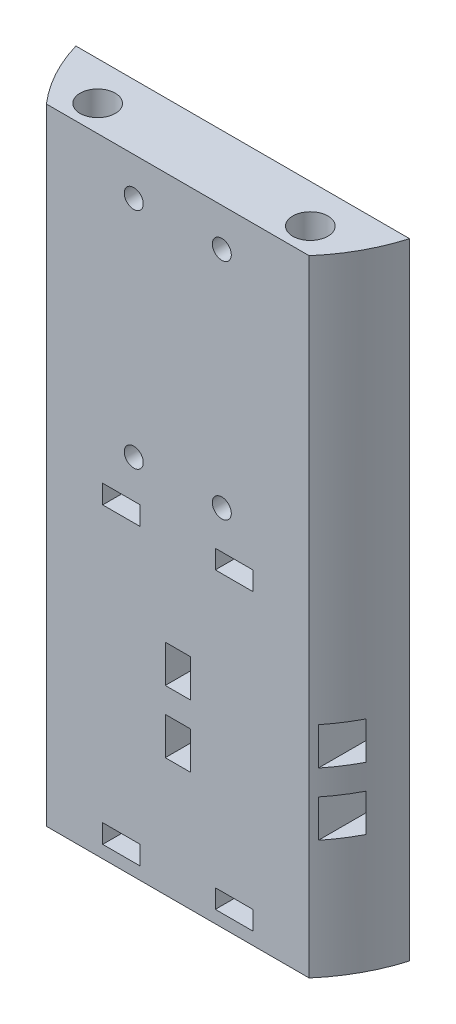
SolidWorks part; units mm, degrees
ref_plane "Front Plane" through (0, 0, 0) normal (0, 0, 1) x (1, 0, 0)
ref_plane "Top Plane" through (0, 0, 0) normal (0, 1, 0) x (1, 0, 0)
ref_plane "Right Plane" through (0, 0, 0) normal (1, 0, 0) x (0, 0, -1)
sketch "Sketch1" plane through (0, 0, 0) normal (0, 1, 0) x (1, 0, 0)
  line L0 (-33.876, -9.9465) -> (33.876, -9.9465)
  line L1 (-26.67, -23.1349) -> (26.67, -23.1349)
  arc A0 (26.67, -23.1349) -> (33.876, -9.9465) centre (0, 0) ccw
  arc A1 (-33.876, -9.9465) -> (-26.67, -23.1349) centre (0, 0) ccw
  point P1 (0, -9.9465)
  dimension "D1" = 70.612
  dimension "D4" = 35.306
  dimension "D2" = 53.34
  dimension "D3" = 67.7519
  dimension "D5" = 9.9465
extrude "Boss-Extrude1" add sketch "Sketch1" along normal blind 127
sketch "Sketch2" plane through (0, 0, 0) normal (0, 1, 0) x (1, 0, 0)
  circle A0 centre (0, 0) radius 35.306
  dimension "D1" = 70.612
sketch "Sketch3" plane through (0, 0, 0) normal (0, 1, 0) x (1, 0, 0)
  circle A0 centre (0, 0) radius 36.576
  dimension "D1" = 73.152
ref_plane "Raft Top" through (0, 0, 9.9465) normal (0, 0, -1) x (-1, 0, 0)
sketch "Sketch10" plane through (0, 0, 9.9465) normal (0, 0, -1) x (-1, 0, 0)
  line L0 (-31.336, 2.54) -> (-31.336, 66.04)
  line L5 (-31.336, 66.04) -> (31.336, 66.04)
  line L10 (31.336, 66.04) -> (31.336, 2.54)
  line L11 (31.336, 2.54) -> (-31.336, 2.54)
  line L16 (33.876, 127) -> (33.876, 0) construction
  line L17 (35.306, 0) -> (-35.306, 0) construction
  line L18 (-33.876, 127) -> (-33.876, 0) construction
  dimension "D1" = 2.54
  dimension "D2" = 2.54
  dimension "D3" = 2.54
  dimension "D4" = 63.5
  dimension "D5" = 62.6719
extrude "Cut-Extrude1" cut sketch "Sketch10" against normal blind 2.54
sketch "Sketch13" plane through (0, 127, 0) normal (0, 1, 0) x (1, 0, 0)
  line L0 (31.336, -12.4865) -> (-31.336, -12.4865) construction
  line L1 (31.336, -12.4865) -> (-31.336, -12.4865)
  line L2 (33.876, -9.9465) -> (-33.876, -9.9465)
  line L3 (-26.67, -23.1349) -> (26.67, -23.1349)
  line L4 (33.876, -9.9465) -> (-33.876, -9.9465)
  line L5 (-26.67, -23.1349) -> (26.67, -23.1349)
  line L6 (-21.59, -12.4865) -> (-21.59, -23.1349) construction
  line L7 (0, -55) -> (0, 55) construction
  arc A2 (-33.876, -9.9465) -> (-26.67, -23.1349) centre (0, 0) ccw
  arc A3 (26.67, -23.1349) -> (33.876, -9.9465) centre (0, 0) ccw
  arc A4 (-33.876, -9.9465) -> (-26.67, -23.1349) centre (0, 0) ccw
  arc A5 (26.67, -23.1349) -> (33.876, -9.9465) centre (0, 0) ccw
  point P10 (-21.59, -17.8107)
  point P13 (21.59, -17.8107)
  dimension "D2" = 21.59
  dimension "D1" = 0
hole_wizard "1/4 Clearance Hole1" positions "Sketch14" profile "Sketch15" hole size "1/4" standard "ANSI Inch" end condition through all
sketch "Sketch14" plane through (0, 127, 0) normal (0, 1, 0) x (1, 0, 0)
  point P0 (-21.59, -17.8107)
  point P3 (21.59, -17.8107)
sketch "Sketch15" plane through (-21.59, 127, 17.8107) normal (1, 0, 0) x (0, 0, 1)
  line L0 (0, 0) -> (0, 127)
  line L1 (0, 127) -> (3.5712, 127)
  line L2 (3.5712, 127) -> (3.5712, 0)
  line L5 (3.5712, 0) -> (0, 0)
  line L11 (0, -6.35) -> (0, 107.95) construction
  dimension "Thru Hole Dia." = 7.1425
  dimension "Thru Hole Depth" = 127
sketch "Sketch16" plane through (0, 0, 9.9465) normal (0, 0, -1) x (-1, 0, 0)
  line L0 (-24.939, 119.253) -> (-8.937, 73.787) construction
  line L1 (-33.876, 96.52) -> (0, 96.52) construction
  line L2 (-33.876, 127) -> (-33.876, 0) construction
  line L3 (0, 40.2336) -> (0, -40.2336) construction
  line L4 (-18.0188, 127) -> (-18.0188, 66.04) construction
  line L5 (31.336, 66.04) -> (-31.336, 66.04) construction
  point P0 (-24.939, 119.253)
  point P1 (-8.937, 119.253)
  point P2 (-8.937, 73.787)
  point P3 (-24.939, 73.787)
  point P4 (-16.938, 96.52)
  point P11 (-16.938, 96.52)
  point P26 (-18.0188, 96.52)
  point P28 (8.937, 73.787)
  point P29 (24.939, 73.787)
  point P30 (8.937, 119.253)
  point P31 (24.939, 119.253)
  dimension "D1" = 16.002
  dimension "D2" = 45.466
sketch "Sketch19" plane through (0, 0, 9.9465) normal (0, 0, -1) x (-1, 0, 0)
  line L0 (0, 66.04) -> (0, 2.54) construction
  line L1 (31.336, 66.04) -> (-31.336, 66.04) construction
  line L2 (-31.336, 2.54) -> (31.336, 2.54) construction
  line L3 (-31.336, 34.29) -> (31.336, 34.29) construction
  line L8 (-2.54, 44.45) -> (2.54, 44.45)
  line L9 (-2.54, 44.45) -> (-2.54, 36.83)
  line L10 (-2.54, 36.83) -> (2.54, 36.83)
  line L11 (2.54, 44.45) -> (2.54, 36.83)
  line L12 (-31.336, 66.04) -> (-31.336, 2.54) construction
  line L13 (31.336, 2.54) -> (31.336, 66.04) construction
  line L14 (-2.54, 31.75) -> (2.54, 31.75)
  line L15 (2.54, 24.13) -> (2.54, 31.75)
  line L16 (-2.54, 24.13) -> (2.54, 24.13)
  line L17 (-2.54, 24.13) -> (-2.54, 31.75)
  line L18 (31.336, 66.04) -> (-31.336, 66.04) construction
  line L19 (31.336, 36.83) -> (27.526, 36.83)
  line L20 (-15.24, 66.04) -> (-7.62, 66.04)
  line L21 (-15.24, 66.04) -> (-15.24, 62.23)
  line L22 (-15.24, 62.23) -> (-7.62, 62.23)
  line L23 (-7.62, 66.04) -> (-7.62, 62.23)
  line L36 (15.24, 62.23) -> (7.62, 62.23)
  line L37 (7.62, 66.04) -> (7.62, 62.23)
  line L38 (15.24, 66.04) -> (7.62, 66.04)
  line L39 (15.24, 66.04) -> (15.24, 62.23)
  line L40 (-15.24, 6.35) -> (-7.62, 6.35)
  line L41 (-7.62, 2.54) -> (-7.62, 6.35)
  line L42 (-15.24, 2.54) -> (-7.62, 2.54)
  line L43 (-15.24, 2.54) -> (-15.24, 6.35)
  line L44 (15.24, 2.54) -> (15.24, 6.35)
  line L45 (15.24, 2.54) -> (7.62, 2.54)
  line L46 (7.62, 2.54) -> (7.62, 6.35)
  line L47 (15.24, 6.35) -> (7.62, 6.35)
  line L48 (-31.336, 44.45) -> (-27.526, 44.45)
  line L49 (-31.336, 44.45) -> (-31.336, 36.83)
  line L50 (-31.336, 36.83) -> (-27.526, 36.83)
  line L51 (-27.526, 44.45) -> (-27.526, 36.83)
  line L52 (27.526, 44.45) -> (27.526, 36.83)
  line L53 (31.336, 44.45) -> (27.526, 44.45)
  line L54 (31.336, 44.45) -> (31.336, 36.83)
  line L55 (31.336, 24.13) -> (31.336, 31.75)
  line L56 (31.336, 24.13) -> (27.526, 24.13)
  line L57 (27.526, 24.13) -> (27.526, 31.75)
  line L58 (31.336, 31.75) -> (27.526, 31.75)
  line L59 (-31.336, 31.75) -> (-27.526, 31.75)
  line L60 (-27.526, 24.13) -> (-27.526, 31.75)
  line L61 (-31.336, 24.13) -> (-27.526, 24.13)
  line L62 (-31.336, 24.13) -> (-31.336, 31.75)
  point P10 (0, 34.29)
  point P12 (-2.54, 44.45)
  point P22 (-15.24, 66.04)
  point P41 (-31.336, 44.45)
  dimension "D1" = 5.08
  dimension "D2" = 7.62
  dimension "D3" = 2.54
  dimension "D4" = 10.16
  dimension "D5" = 15.24
  dimension "D6" = 7.62
  dimension "D7" = 3.81
  dimension "D8" = 10.16
  dimension "D9" = 3.81
  dimension "D10" = 7.62
hole_wizard "#8 Clearance Hole1" positions "Sketch20" profile "Sketch21" hole size "#8" standard "ANSI Inch" end condition through all
sketch "Sketch20" plane through (0, 0, 9.9465) normal (0, 0, -1) x (-1, 0, 0)
  point P3 (-8.937, 119.253)
  point P9 (-8.937, 73.787)
  point P12 (8.937, 73.787)
  point P21 (8.937, 119.253)
  point P30 (0, 0)
  point P31 (0, 0)
sketch "Sketch21" plane through (8.937, 119.253, 9.9465) normal (1, 0, 0) x (0, 1, 0)
  line L0 (0, 0) -> (0, 13.1884)
  line L1 (0, 13.1884) -> (1.9304, 13.1884)
  line L2 (1.9304, 13.1884) -> (1.9304, 0)
  line L5 (1.9304, 0) -> (0, 0)
  line L11 (0, -6.35) -> (0, 107.95) construction
  dimension "Thru Hole Dia." = 3.8608
  dimension "Thru Hole Depth" = 13.1884
extrude "Cut-Extrude3" cut sketch "Sketch19" against normal through all
hole_wizard "#8 Clearance Hole2" positions "Sketch22" profile "Sketch24" hole size "#8" standard "ANSI Inch"
sketch "Sketch22" plane through (0, 0, 9.9465) normal (0, 0, -1) x (-1, 0, 0)
  point P0 (-24.939, 119.253)
  point P3 (-24.939, 73.787)
  point P6 (24.939, 73.787)
  point P9 (24.939, 119.253)
sketch "Sketch24" plane through (24.939, 119.253, 9.9465) normal (1, 0, 0) x (0, 1, 0)
  line L0 (0, 0) -> (0, 3.81)
  line L1 (0, 3.81) -> (1.9304, 3.81)
  line L2 (1.9304, 3.81) -> (1.9304, 0)
  line L5 (1.9304, 0) -> (0, 0)
  line L10 (0, 3.81) -> (-1.9304, 3.81) construction
  line L11 (0, -6.35) -> (0, 107.95) construction
  dimension "Hole Dia." = 3.8608
  dimension "Hole Depth" = 3.81
  dimension "Drill Angle" = 180
